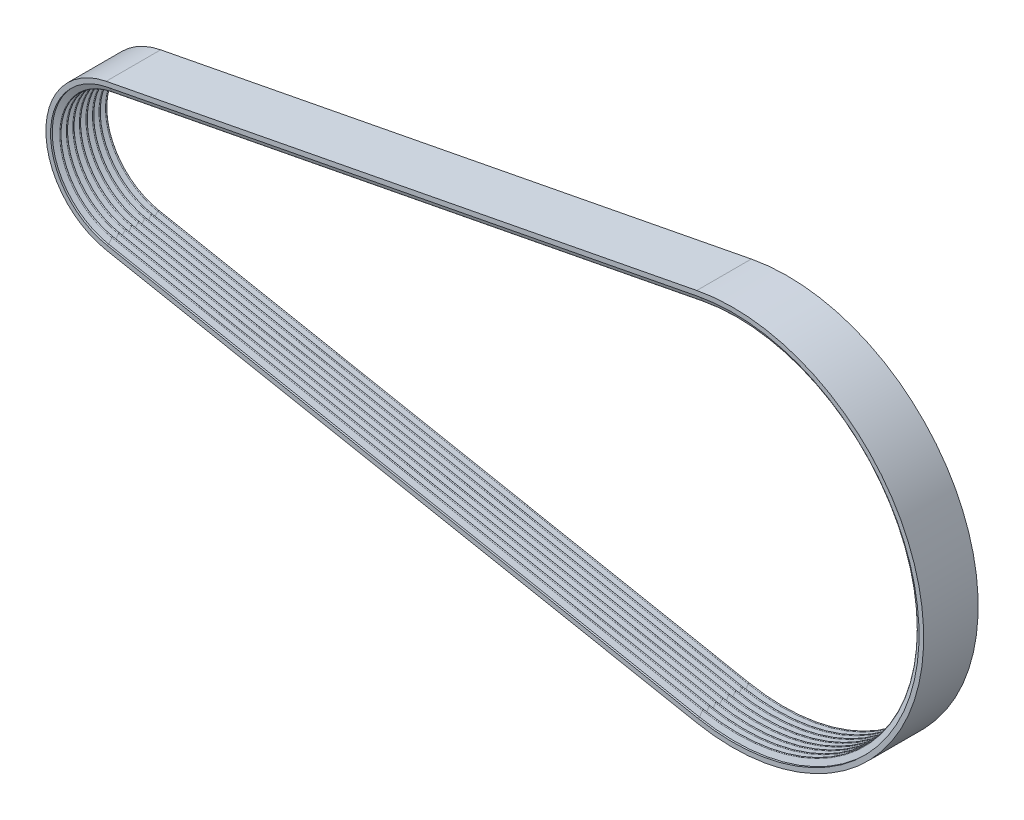
SolidWorks part; units mm, degrees
material "Rubber"
ref_plane "Front Plane" through (0, 0, 0) normal (0, 0, 1) x (1, 0, 0)
ref_plane "Top Plane" through (0, 0, 0) normal (0, 1, 0) x (1, 0, 0)
ref_plane "Right Plane" through (0, 0, 0) normal (1, 0, 0) x (0, 0, -1)
sketch "Sketch1" plane through (0, 0, 0) normal (0, 0, 1) x (1, 0, 0)
  line L0 (0, 0) -> (334.6196, 0) construction
  line L1 (55, 0) -> (-55, 0) construction
  line L2 (-7.2302, 37.4077) -> (315.3392, 99.7538)
  line L3 (315.3392, -99.7538) -> (-7.2302, -37.4077)
  arc A0 (-7.2302, 37.4077) -> (-7.2302, -37.4077) centre (0, 0) ccw
  arc A1 (315.3392, 99.7538) -> (315.3392, -99.7538) centre (334.6196, 0) cw
  dimension "D2" = 38.1
  dimension "D3" = 101.6
  dimension "D1" = 334.6196
ref_plane "Plane1" through (-7.2302, 37.4077, 0) normal (0.9818, 0.1898, 0) x (0, 0, -1)
sketch "Sketch2" plane through (-7.2302, 37.4077, 0) normal (0.9818, 0.1898, 0) x (0, 0, -1)
  line L0 (0, 0) -> (0, -3.2869) construction
  line L1 (0, 2.54) -> (14.8794, 2.54)
  line L2 (0, 2.54) -> (0, 0.2507)
  line L3 (14.8794, 2.54) -> (14.8794, 0)
  line L4 (13.9269, 0) -> (14.8794, 0)
  line L6 (0.358, 0) -> (-0.358, 0) construction
  line L7 (3.5712, -0.1303) -> (0, -0.1303) construction
  line L8 (0, -0.1303) -> (0, 0) construction
  line L9 (0, 0) -> (0, 0.2507) construction
  line L14 (12.1413, -2.9386) -> (9.2861, -2.9386) construction
  line L15 (8.5701, -2.9386) -> (5.7149, -2.9386) construction
  line L16 (4.9988, -2.9386) -> (2.1436, -2.9386) construction
  line L18 (0.358, 0) -> (3.2132, 0) construction
  line L19 (0.358, 0) -> (1.4276, -2.9386)
  line L20 (3.2132, 0) -> (3.9293, 0) construction
  line L21 (2.1436, -2.9386) -> (3.2132, 0)
  line L22 (3.9293, 0) -> (6.7845, 0) construction
  line L23 (3.9293, 0) -> (4.9988, -2.9386)
  line L24 (6.7845, 0) -> (7.5005, 0) construction
  line L25 (5.7149, -2.9386) -> (6.7845, 0)
  line L26 (7.5005, 0) -> (10.3557, 0) construction
  line L27 (7.5005, 0) -> (8.5701, -2.9386)
  line L28 (11.0717, 0) -> (13.9269, 0) construction
  line L29 (9.2861, -2.9386) -> (10.3557, 0)
  line L31 (11.0717, 0) -> (12.1413, -2.9386)
  line L33 (12.8574, -2.9386) -> (13.9269, 0)
  arc A0 (12.1413, -2.9386) -> (12.8574, -2.9386) centre (12.4993, -2.8083) ccw
  arc A1 (11.0717, 0) -> (10.3557, 0) centre (10.7137, -0.1303) ccw
  arc A2 (8.5701, -2.9386) -> (9.2861, -2.9386) centre (8.9281, -2.8083) ccw
  arc A3 (4.9988, -2.9386) -> (5.7149, -2.9386) centre (5.3569, -2.8083) ccw
  arc A4 (1.4276, -2.9386) -> (2.1436, -2.9386) centre (1.7856, -2.8083) ccw
  arc A5 (0.358, 0) -> (0, 0.2507) centre (0, -0.1303) ccw
  arc A13 (3.9293, 0) -> (3.2132, 0) centre (3.5712, -0.1303) ccw
  arc A14 (7.5005, 0) -> (6.7845, 0) centre (7.1425, -0.1303) ccw
  dimension "D6" = 2.54
  dimension "D2" = 0.381
  dimension "D1" = 0.9525
  dimension "D3" = 3.5712
  dimension "D4" = 20
sweep "Sweep1" add profiles "Sketch2" path "Sketch1"
mirror "Mirror1" of "Sweep1"
